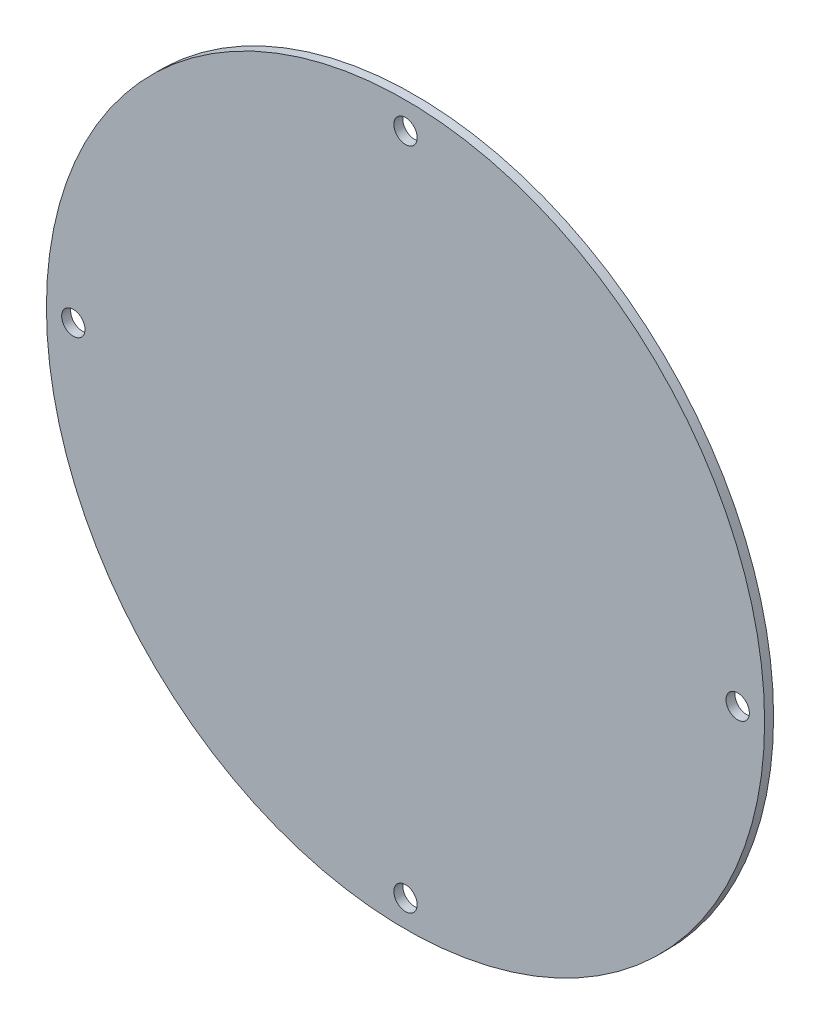
SolidWorks part; units mm, degrees
material "Alliage 1060"
ref_plane "Plan de face" through (0, 0, 0) normal (0, 0, 1) x (1, 0, 0)
ref_plane "Plan de dessus" through (0, 0, 0) normal (0, 1, 0) x (1, 0, 0)
ref_plane "Plan de droite" through (0, 0, 0) normal (1, 0, 0) x (0, 0, -1)
sketch "Esquisse1" plane through (0, 0, 0) normal (0, 0, 1) x (1, 0, 0)
  circle A0 centre (0, 0) radius 40
  dimension "D1" = 80
extrude "Boss.-Extru.1" add sketch "Esquisse1" along normal blind 1
hole_wizard "Dégagement M21" positions "Esquisse4" profile "Esquisse3" hole size "M2" standard "ISO" end condition through all
sketch "Esquisse4" plane through (0, 0, 0) normal (0, 0, -1) x (-1, 0, 0)
  point P0 (0, 37)
  dimension "D1" = 37
sketch "Esquisse3" plane through (0, 37, 0) normal (1, 0, 0) x (0, 1, 0)
  line L0 (0, 0) -> (0, 1)
  line L1 (0, 1) -> (1.3, 1)
  line L2 (1.3, 1) -> (1.3, 0)
  line L5 (1.3, 0) -> (0, 0)
  line L11 (0, -6.35) -> (0, 107.95) construction
  dimension "Diamètre du perçage jusqu'au prochain" = 2.6
  dimension "Profondeur du perçage jusqu'au prochain" = 1
pattern_circular "Répétition circulaire1" count 4 over 360 about axis through (0, 0, 0) along (0, 0, 1) of "Dégagement M21"
